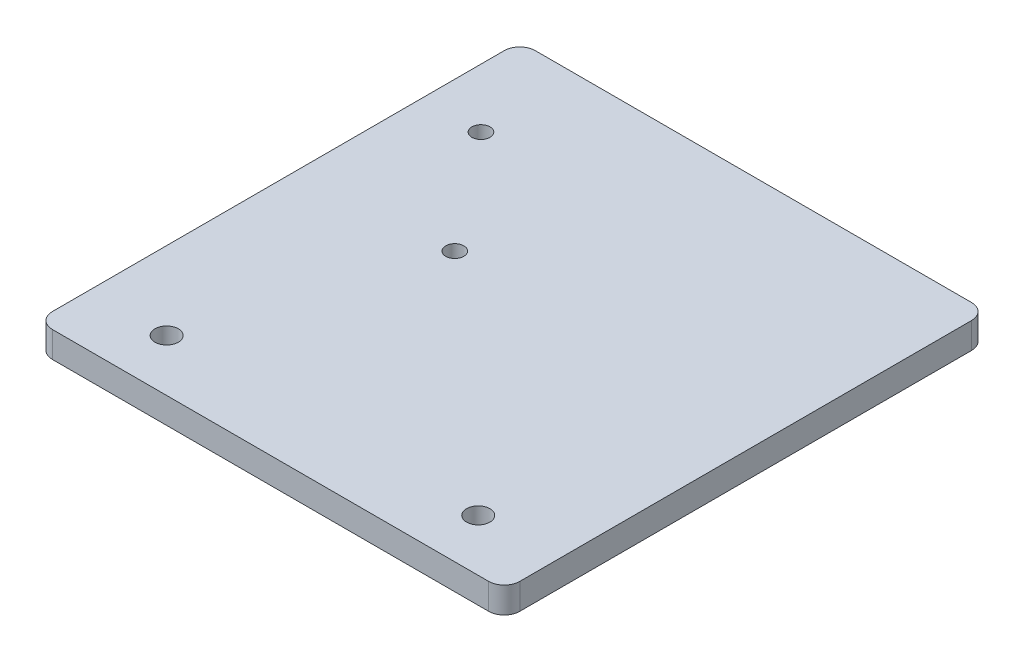
SolidWorks part; units mm, degrees
ref_plane "Front Plane" through (0, 0, 0) normal (0, 0, 1) x (1, 0, 0)
ref_plane "Top Plane" through (0, 0, 0) normal (0, 1, 0) x (1, 0, 0)
ref_plane "Right Plane" through (0, 0, 0) normal (1, 0, 0) x (0, 0, -1)
sketch "Sketch1" plane through (0, 0, 0) normal (0, 1, 0) x (1, 0, 0)
  line L1 (-45, 46.5) -> (45, 46.5)
  line L2 (-45, 46.5) -> (-45, -46.5)
  line L3 (-45, -46.5) -> (45, -46.5)
  line L4 (45, 46.5) -> (45, -46.5)
  line L5 (-45, 46.5) -> (45, -46.5) construction
  line L6 (-45, -46.5) -> (45, 46.5) construction
  line L7 (-45, -46.5) -> (45, -46.5) construction
  line L8 (-45, -46.5) -> (-45, -26.5) construction
  line L9 (-45, -26.5) -> (45, -26.5) construction
  line L10 (45, -46.5) -> (45, -26.5) construction
  line L11 (0, -26.5) -> (0, -46.5) construction
  line L12 (-45, -36.5) -> (45, -36.5) construction
  line L13 (-33.66, 27.68) -> (-16.34, 27.68) construction
  line L14 (-33.66, 27.68) -> (-33.66, 5.32) construction
  line L15 (-33.66, 5.32) -> (-16.34, 5.32) construction
  line L16 (-16.34, 27.68) -> (-16.34, 5.32) construction
  line L17 (-25, 5.32) -> (-25, 27.68) construction
  line L18 (-33.66, 16.5) -> (-16.34, 16.5) construction
  circle A0 centre (-30, -36.5) radius 2.25
  circle A1 centre (30, -36.5) radius 2.25
  circle A2 centre (-33.66, 27.68) radius 1.75
  circle A3 centre (-16.34, 5.32) radius 1.75
  point P0 (0, 0)
  point P142 (-25, 16.5)
  point P292 (0, -36.5)
  dimension "D4" = 4.5
  dimension "D10" = 3.5
  dimension "D1" = 93
  dimension "D2" = 90
  dimension "D3" = 20
  dimension "D5" = 60
  dimension "D6" = 22.36
  dimension "D7" = 17.32
  dimension "D8" = 43
  dimension "D9" = 20
extrude "Boss-Extrude1" add sketch "Sketch1" along normal blind 5
fillet "Fillet1" radius 3 4 edges at (45, 2.5, 46.5) (-45, 2.5, 46.5) (45, 2.5, -46.5) (-45, 2.5, -46.5)
